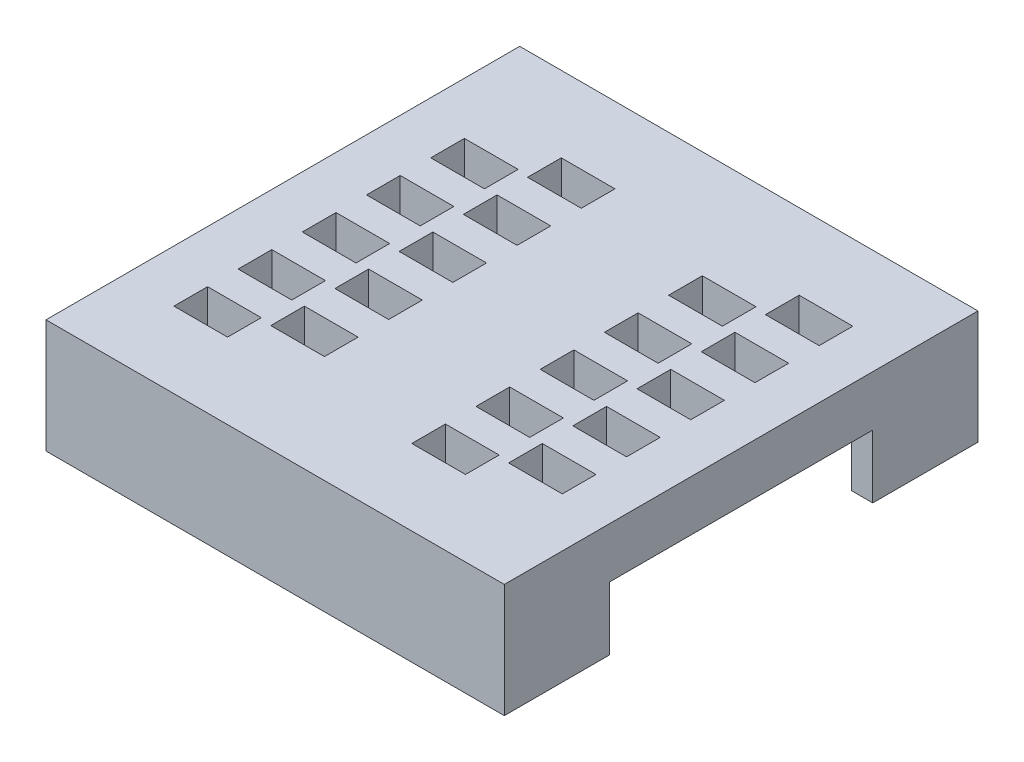
SolidWorks part; units mm, degrees
ref_plane "Спереди" through (0, 0, 0) normal (0, 0, 1) x (1, 0, 0)
ref_plane "Сверху" through (0, 0, 0) normal (0, 1, 0) x (1, 0, 0)
ref_plane "Справа" through (0, 0, 0) normal (1, 0, 0) x (0, 0, -1)
sketch "Эскиз1" plane through (0, 0, 0) normal (0, 1, 0) x (1, 0, 0)
  line L0 (2.8031, 2.5812) -> (46.3427, 2.5812)
  line L1 (46.3427, 2.5812) -> (46.3427, 47.5812)
  line L2 (46.3427, 47.5812) -> (2.8031, 47.5812)
  line L3 (2.8031, 47.5812) -> (2.8031, 2.5812)
  line L5 (13.9531, 37.1809) -> (19.0531, 37.1809)
  line L6 (13.9531, 37.1809) -> (13.9531, 40.3809)
  line L7 (13.9531, 40.3809) -> (19.0531, 40.3809)
  line L8 (19.0531, 37.1809) -> (19.0531, 40.3809)
  line L9 (13.9531, 37.1809) -> (19.0531, 40.3809) construction
  line L10 (13.9531, 40.3809) -> (19.0531, 37.1809) construction
  line L11 (36.5531, 37.1809) -> (41.6531, 37.1809)
  line L12 (36.5531, 37.1809) -> (36.5531, 40.3809)
  line L13 (36.5531, 40.3809) -> (41.6531, 40.3809)
  line L14 (41.6531, 37.1809) -> (41.6531, 40.3809)
  line L15 (36.5531, 37.1809) -> (41.6531, 40.3809) construction
  line L16 (36.5531, 40.3809) -> (41.6531, 37.1809) construction
  line L17 (7.7531, 34.1809) -> (12.8531, 34.1809)
  line L18 (7.7531, 34.1809) -> (7.7531, 37.3809)
  line L19 (7.7531, 37.3809) -> (12.8531, 37.3809)
  line L20 (12.8531, 34.1809) -> (12.8531, 37.3809)
  line L21 (7.7531, 34.1809) -> (12.8531, 37.3809) construction
  line L22 (7.7531, 37.3809) -> (12.8531, 34.1809) construction
  line L23 (30.3531, 34.1809) -> (35.4531, 34.1809)
  line L24 (30.3531, 34.1809) -> (30.3531, 37.3809)
  line L25 (30.3531, 37.3809) -> (35.4531, 37.3809)
  line L26 (35.4531, 34.1809) -> (35.4531, 37.3809)
  line L27 (30.3531, 34.1809) -> (35.4531, 37.3809) construction
  line L28 (30.3531, 37.3809) -> (35.4531, 34.1809) construction
  line L29 (13.9531, 31.0809) -> (19.0531, 31.0809)
  line L30 (13.9531, 31.0809) -> (13.9531, 34.2809)
  line L31 (13.9531, 34.2809) -> (19.0531, 34.2809)
  line L32 (19.0531, 31.0809) -> (19.0531, 34.2809)
  line L33 (13.9531, 31.0809) -> (19.0531, 34.2809) construction
  line L34 (13.9531, 34.2809) -> (19.0531, 31.0809) construction
  line L35 (36.5531, 31.0809) -> (41.6531, 31.0809)
  line L36 (36.5531, 31.0809) -> (36.5531, 34.2809)
  line L37 (36.5531, 34.2809) -> (41.6531, 34.2809)
  line L38 (41.6531, 31.0809) -> (41.6531, 34.2809)
  line L39 (36.5531, 31.0809) -> (41.6531, 34.2809) construction
  line L40 (36.5531, 34.2809) -> (41.6531, 31.0809) construction
  line L41 (7.7531, 28.0809) -> (12.8531, 28.0809)
  line L42 (7.7531, 28.0809) -> (7.7531, 31.2809)
  line L43 (7.7531, 31.2809) -> (12.8531, 31.2809)
  line L44 (12.8531, 28.0809) -> (12.8531, 31.2809)
  line L45 (7.7531, 28.0809) -> (12.8531, 31.2809) construction
  line L46 (7.7531, 31.2809) -> (12.8531, 28.0809) construction
  line L47 (30.3531, 28.0809) -> (35.4531, 28.0809)
  line L48 (30.3531, 28.0809) -> (30.3531, 31.2809)
  line L49 (30.3531, 31.2809) -> (35.4531, 31.2809)
  line L50 (35.4531, 28.0809) -> (35.4531, 31.2809)
  line L51 (30.3531, 28.0809) -> (35.4531, 31.2809) construction
  line L52 (30.3531, 31.2809) -> (35.4531, 28.0809) construction
  line L53 (41.6531, 24.9809) -> (36.5531, 24.9809)
  line L54 (41.6531, 24.9809) -> (41.6531, 28.1809)
  line L55 (41.6531, 28.1809) -> (36.5531, 28.1809)
  line L56 (36.5531, 24.9809) -> (36.5531, 28.1809)
  line L57 (41.6531, 24.9809) -> (36.5531, 28.1809) construction
  line L58 (41.6531, 28.1809) -> (36.5531, 24.9809) construction
  line L59 (19.0531, 24.9809) -> (13.9531, 24.9809)
  line L60 (19.0531, 24.9809) -> (19.0531, 28.1809)
  line L61 (19.0531, 28.1809) -> (13.9531, 28.1809)
  line L62 (13.9531, 24.9809) -> (13.9531, 28.1809)
  line L63 (19.0531, 24.9809) -> (13.9531, 28.1809) construction
  line L64 (19.0531, 28.1809) -> (13.9531, 24.9809) construction
  line L65 (7.7531, 21.9809) -> (12.8531, 21.9809)
  line L66 (7.7531, 21.9809) -> (7.7531, 25.1809)
  line L67 (7.7531, 25.1809) -> (12.8531, 25.1809)
  line L68 (12.8531, 21.9809) -> (12.8531, 25.1809)
  line L69 (7.7531, 21.9809) -> (12.8531, 25.1809) construction
  line L70 (7.7531, 25.1809) -> (12.8531, 21.9809) construction
  line L71 (30.3531, 21.9809) -> (35.4531, 21.9809)
  line L72 (30.3531, 21.9809) -> (30.3531, 25.1809)
  line L73 (30.3531, 25.1809) -> (35.4531, 25.1809)
  line L74 (35.4531, 21.9809) -> (35.4531, 25.1809)
  line L75 (30.3531, 21.9809) -> (35.4531, 25.1809) construction
  line L76 (30.3531, 25.1809) -> (35.4531, 21.9809) construction
  line L77 (41.6531, 18.8809) -> (36.5531, 18.8809)
  line L78 (41.6531, 18.8809) -> (41.6531, 22.0809)
  line L79 (41.6531, 22.0809) -> (36.5531, 22.0809)
  line L80 (36.5531, 18.8809) -> (36.5531, 22.0809)
  line L81 (41.6531, 18.8809) -> (36.5531, 22.0809) construction
  line L82 (41.6531, 22.0809) -> (36.5531, 18.8809) construction
  line L83 (19.0531, 18.8809) -> (13.9531, 18.8809)
  line L84 (10.3031, 49.6407) -> (10.3031, -1.549) construction
  line L85 (16.5031, 49.6407) -> (16.5031, -1.4408) construction
  line L86 (32.9031, 49.6407) -> (32.9031, -1.6572) construction
  line L87 (39.1031, 49.6407) -> (39.1031, -2.7395) construction
  line L88 (1.0994, 38.7809) -> (49.6918, 38.7809) construction
  line L89 (1.0994, 35.7809) -> (49.6918, 35.7809) construction
  line L90 (49.6918, 32.6809) -> (1.0994, 32.6809) construction
  line L91 (1.0994, 29.6809) -> (49.6918, 29.6809) construction
  line L92 (49.6918, 26.5809) -> (1.0994, 26.5809) construction
  line L93 (0.7747, 23.5809) -> (49.6918, 23.5809) construction
  line L94 (49.6918, 20.4809) -> (0.7747, 20.4809) construction
  line L95 (0.7747, 17.4809) -> (49.6918, 17.4809) construction
  line L96 (49.6918, 14.3809) -> (0.7747, 14.3809) construction
  line L97 (-6.1228, 11.3809) -> (51.4369, 11.3809) construction
  line L98 (19.0531, 18.8809) -> (19.0531, 22.0809)
  line L99 (19.0531, 22.0809) -> (13.9531, 22.0809)
  line L100 (13.9531, 18.8809) -> (13.9531, 22.0809)
  line L101 (19.0531, 18.8809) -> (13.9531, 22.0809) construction
  line L102 (19.0531, 22.0809) -> (13.9531, 18.8809) construction
  line L103 (35.4531, 15.8809) -> (30.3531, 15.8809)
  line L104 (35.4531, 15.8809) -> (35.4531, 19.0809)
  line L105 (35.4531, 19.0809) -> (30.3531, 19.0809)
  line L106 (30.3531, 15.8809) -> (30.3531, 19.0809)
  line L107 (35.4531, 15.8809) -> (30.3531, 19.0809) construction
  line L108 (35.4531, 19.0809) -> (30.3531, 15.8809) construction
  line L109 (12.8531, 15.8809) -> (7.7531, 15.8809)
  line L110 (12.8531, 15.8809) -> (12.8531, 19.0809)
  line L111 (12.8531, 19.0809) -> (7.7531, 19.0809)
  line L112 (7.7531, 15.8809) -> (7.7531, 19.0809)
  line L113 (12.8531, 15.8809) -> (7.7531, 19.0809) construction
  line L114 (12.8531, 19.0809) -> (7.7531, 15.8809) construction
  line L115 (19.0531, 12.7809) -> (13.9531, 12.7809)
  line L116 (19.0531, 12.7809) -> (19.0531, 15.9809)
  line L117 (19.0531, 15.9809) -> (13.9531, 15.9809)
  line L118 (13.9531, 12.7809) -> (13.9531, 15.9809)
  line L119 (19.0531, 12.7809) -> (13.9531, 15.9809) construction
  line L120 (19.0531, 15.9809) -> (13.9531, 12.7809) construction
  line L121 (7.7531, 9.7809) -> (12.8531, 9.7809)
  line L122 (7.7531, 9.7809) -> (7.7531, 12.9809)
  line L123 (7.7531, 12.9809) -> (12.8531, 12.9809)
  line L124 (12.8531, 9.7809) -> (12.8531, 12.9809)
  line L125 (7.7531, 9.7809) -> (12.8531, 12.9809) construction
  line L126 (7.7531, 12.9809) -> (12.8531, 9.7809) construction
  line L127 (30.3531, 9.7809) -> (35.4531, 9.7809)
  line L128 (30.3531, 9.7809) -> (30.3531, 12.9809)
  line L129 (30.3531, 12.9809) -> (35.4531, 12.9809)
  line L130 (35.4531, 9.7809) -> (35.4531, 12.9809)
  line L131 (30.3531, 9.7809) -> (35.4531, 12.9809) construction
  line L132 (30.3531, 12.9809) -> (35.4531, 9.7809) construction
  line L133 (36.5531, 12.7809) -> (41.6531, 12.7809)
  line L134 (36.5531, 12.7809) -> (36.5531, 15.9809)
  line L135 (36.5531, 15.9809) -> (41.6531, 15.9809)
  line L136 (41.6531, 12.7809) -> (41.6531, 15.9809)
  line L137 (36.5531, 12.7809) -> (41.6531, 15.9809) construction
  line L138 (36.5531, 15.9809) -> (41.6531, 12.7809) construction
  point P7 (16.5031, 38.7809)
  point P12 (39.1031, 38.7809)
  point P17 (10.3031, 35.7809)
  point P22 (32.9031, 35.7809)
  point P27 (16.5031, 32.6809)
  point P32 (39.1031, 32.6809)
  point P37 (10.3031, 29.6809)
  point P42 (32.9031, 29.6809)
  point P47 (39.1031, 26.5809)
  point P52 (16.5031, 26.5809)
  point P57 (10.3031, 23.5809)
  point P62 (32.9031, 23.5809)
  point P67 (39.1031, 20.4809)
  point P72 (16.5031, 20.4809)
  point P77 (32.9031, 17.4809)
  point P82 (10.3031, 17.4809)
  point P112 (16.5031, 14.3809)
  point P117 (10.3031, 11.3809)
  point P122 (32.9031, 11.3809)
  point P127 (39.1031, 14.3809)
  dimension "D1" = 43.5396
  dimension "D2" = 45
  dimension "D3" = 7.5
  dimension "D4" = 6.2
  dimension "D5" = 16.4
  dimension "D6" = 6.2
  dimension "D7" = 8.8003
  dimension "D8" = 3
  dimension "D9" = 3.1
  dimension "D10" = 3
  dimension "D11" = 3.1
  dimension "D12" = 3
  dimension "D13" = 3.1
  dimension "D14" = 3
  dimension "D15" = 3.1
  dimension "D16" = 3
  dimension "D17" = 3.2
  dimension "D18" = 5.1
extrude "Бобышка-Вытянуть1" add sketch "Эскиз1" along normal blind 3.2
sketch "Эскиз2" plane through (0, 0, 0) normal (0, 1, 0) x (1, 0, 0)
  line L1 (2.8031, 47.5812) -> (46.3427, 47.5812)
  line L2 (2.8031, 47.5812) -> (2.8031, 2.5812)
  line L3 (2.8031, 2.5812) -> (46.3427, 2.5812)
  line L4 (-1.1216, 42.5812) -> (57.6795, 42.5812) construction
  line L5 (46.3427, 47.5812) -> (46.3427, 2.5812)
  line L65 (-1.6798, 7.5812) -> (52.4692, 7.5812) construction
  line L66 (7.8031, 55.0464) -> (7.8031, -0.7774) construction
  line L67 (41.3427, 54.5812) -> (41.3427, -0.6844) construction
  line L68 (2.8031, 47.5812) -> (2.8031, 2.5812) construction
  line L69 (46.3427, 2.5812) -> (46.3427, 47.5812) construction
  line L70 (46.3427, 47.5812) -> (2.8031, 47.5812) construction
  line L71 (2.8031, 2.5812) -> (46.3427, 2.5812) construction
  line L72 (16.5031, 50.8599) -> (16.5031, 0.0003) construction
  line L89 (32.9031, 50.8599) -> (32.9031, -1.0562) construction
  line L90 (-0.3772, 38.7812) -> (21.6731, 38.7812) construction
  line L91 (21.6731, 32.6812) -> (-0.3772, 32.6812) construction
  line L92 (21.6731, 26.5812) -> (-0.3772, 26.5812) construction
  line L93 (21.6731, 20.4812) -> (-0.3772, 20.4812) construction
  line L94 (21.6731, 14.3812) -> (-0.3772, 14.3812) construction
  line L95 (26.2321, 11.3812) -> (49.1198, 11.3812) construction
  line L96 (26.2321, 17.4812) -> (49.1198, 17.4812) construction
  line L97 (26.2321, 23.5812) -> (49.1198, 23.5812) construction
  line L98 (26.2321, 29.6812) -> (49.1198, 29.6812) construction
  line L99 (25.953, 35.7812) -> (49.1198, 35.7812) construction
  line L101 (13.7031, 35.9812) -> (19.3031, 35.9812)
  line L102 (13.7031, 35.9812) -> (13.7031, 41.5812)
  line L103 (13.7031, 41.5812) -> (19.3031, 41.5812)
  line L104 (19.3031, 35.9812) -> (19.3031, 41.5812)
  line L105 (13.7031, 35.9812) -> (19.3031, 41.5812) construction
  line L106 (13.7031, 41.5812) -> (19.3031, 35.9812) construction
  line L107 (13.7031, 29.8241) -> (19.3031, 29.8241)
  line L108 (13.7031, 29.8241) -> (13.7031, 35.4241)
  line L109 (13.7031, 35.4241) -> (19.3031, 35.4241)
  line L110 (19.3031, 29.8241) -> (19.3031, 35.4241)
  line L111 (13.7031, 29.8241) -> (19.3031, 35.4241) construction
  line L112 (13.7031, 35.4241) -> (19.3031, 29.8241) construction
  line L113 (13.7031, 23.7812) -> (19.3031, 23.7812)
  line L114 (13.7031, 23.7812) -> (13.7031, 29.3812)
  line L115 (13.7031, 29.3812) -> (19.3031, 29.3812)
  line L116 (19.3031, 23.7812) -> (19.3031, 29.3812)
  line L117 (13.7031, 23.7812) -> (19.3031, 29.3812) construction
  line L118 (13.7031, 29.3812) -> (19.3031, 23.7812) construction
  line L119 (13.7031, 17.6812) -> (19.3031, 17.6812)
  line L120 (13.7031, 17.6812) -> (13.7031, 23.2812)
  line L121 (13.7031, 23.2812) -> (19.3031, 23.2812)
  line L122 (19.3031, 17.6812) -> (19.3031, 23.2812)
  line L123 (13.7031, 17.6812) -> (19.3031, 23.2812) construction
  line L124 (13.7031, 23.2812) -> (19.3031, 17.6812) construction
  line L125 (13.7031, 11.5812) -> (19.3031, 11.5812)
  line L126 (13.7031, 11.5812) -> (13.7031, 17.1812)
  line L127 (13.7031, 17.1812) -> (19.3031, 17.1812)
  line L128 (19.3031, 11.5812) -> (19.3031, 17.1812)
  line L129 (13.7031, 11.5812) -> (19.3031, 17.1812) construction
  line L130 (13.7031, 17.1812) -> (19.3031, 11.5812) construction
  line L131 (35.7031, 8.5812) -> (30.1031, 8.5812)
  line L132 (35.7031, 8.5812) -> (35.7031, 14.1812)
  line L133 (35.7031, 14.1812) -> (30.1031, 14.1812)
  line L134 (30.1031, 8.5812) -> (30.1031, 14.1812)
  line L135 (35.7031, 8.5812) -> (30.1031, 14.1812) construction
  line L136 (35.7031, 14.1812) -> (30.1031, 8.5812) construction
  line L137 (35.7031, 14.6812) -> (30.1031, 14.6812)
  line L138 (35.7031, 14.6812) -> (35.7031, 20.2812)
  line L139 (35.7031, 20.2812) -> (30.1031, 20.2812)
  line L140 (30.1031, 14.6812) -> (30.1031, 20.2812)
  line L141 (35.7031, 14.6812) -> (30.1031, 20.2812) construction
  line L142 (35.7031, 20.2812) -> (30.1031, 14.6812) construction
  line L143 (35.7031, 20.7812) -> (30.1031, 20.7812)
  line L144 (35.7031, 20.7812) -> (35.7031, 26.3812)
  line L145 (35.7031, 26.3812) -> (30.1031, 26.3812)
  line L146 (30.1031, 20.7812) -> (30.1031, 26.3812)
  line L147 (35.7031, 20.7812) -> (30.1031, 26.3812) construction
  line L148 (35.7031, 26.3812) -> (30.1031, 20.7812) construction
  line L149 (35.7031, 26.8812) -> (30.1031, 26.8812)
  line L150 (35.7031, 26.8812) -> (35.7031, 32.4812)
  line L151 (35.7031, 32.4812) -> (30.1031, 32.4812)
  line L152 (30.1031, 26.8812) -> (30.1031, 32.4812)
  line L153 (35.7031, 26.8812) -> (30.1031, 32.4812) construction
  line L154 (35.7031, 32.4812) -> (30.1031, 26.8812) construction
  line L155 (35.7031, 32.9812) -> (30.1031, 32.9812)
  line L156 (35.7031, 32.9812) -> (35.7031, 38.5812)
  line L157 (35.7031, 38.5812) -> (30.1031, 38.5812)
  line L158 (30.1031, 32.9812) -> (30.1031, 38.5812)
  line L159 (35.7031, 32.9812) -> (30.1031, 38.5812) construction
  line L160 (35.7031, 38.5812) -> (30.1031, 32.9812) construction
  circle A4 centre (7.8031, 42.5812) radius 0.5
  circle A5 centre (41.3427, 42.5812) radius 0.5
  circle A6 centre (41.3427, 7.5812) radius 0.5
  circle A7 centre (7.8031, 7.5812) radius 0.5
  point P142 (16.5031, 38.7812)
  point P147 (16.5031, 32.6241)
  point P148 (16.5031, 32.6241)
  point P152 (16.5031, 26.5812)
  point P157 (16.5031, 20.4812)
  point P162 (16.5031, 14.3812)
  point P167 (32.9031, 11.3812)
  point P172 (32.9031, 17.4812)
  point P177 (32.9031, 23.5812)
  point P182 (32.9031, 29.6812)
  point P187 (32.9031, 35.7812)
  dimension "D26" = 1
  dimension "D22" = 5
  dimension "D23" = 5
  dimension "D24" = 5
  dimension "D25" = 5
  dimension "D27" = 6.8
  dimension "D28" = 6.1
  dimension "D29" = 6.1
  dimension "D30" = 6.1
  dimension "D31" = 6.1
  dimension "D32" = 3.8
  dimension "D33" = 6.1
  dimension "D34" = 6.1
  dimension "D35" = 6.1
  dimension "D36" = 6.1
  dimension "D37" = 5.6
  dimension "D38" = 5.6
extrude "Бобышка-Вытянуть3" add sketch "Эскиз2" against normal blind 0.6
sketch "Эскиз3" plane through (0, -0.6, 0) normal (0, -1, 0) x (1, 0, 0)
  circle A0 centre (7.8031, -7.5812) radius 0.5
  circle A1 centre (41.3427, -7.5812) radius 0.5
  circle A2 centre (7.8031, -42.5812) radius 0.5
  circle A3 centre (41.3427, -42.5812) radius 0.5
  circle A4 centre (7.8031, -7.5812) radius 5
  circle A5 centre (41.3427, -7.5812) radius 5
  circle A6 centre (41.3427, -42.5812) radius 5
  circle A7 centre (7.8031, -42.5812) radius 5
  point P15 (41.3427, -42.5812)
  dimension "D1" = 10
  dimension "D2" = 1
extrude "Бобышка-Вытянуть4" add sketch "Эскиз3" along normal blind 1
sketch "Эскиз4" plane through (0, -0.6, 0) normal (0, -1, 0) x (1, 0, 0)
  line L1 (2.8031, -47.5812) -> (46.3427, -47.5812)
  line L2 (2.8031, -47.5812) -> (2.8031, -2.5812)
  line L3 (2.8031, -2.5812) -> (46.3427, -2.5812)
  line L4 (46.3427, -47.5812) -> (46.3427, -2.5812)
  line L5 (4.8031, -4.5812) -> (44.3427, -4.5812)
  line L6 (4.8031, -4.5812) -> (4.8031, -45.5812)
  line L7 (4.8031, -45.5812) -> (44.3427, -45.5812)
  line L8 (44.3427, -4.5812) -> (44.3427, -45.5812)
  dimension "D1" = 2
  dimension "D2" = 2
  dimension "D3" = 2
  dimension "D4" = 2
extrude "Бобышка-Вытянуть6" add sketch "Эскиз4" along normal blind 7
sketch "Эскиз6" plane through (0, -7.6, 0) normal (0, -1, 0) x (1, 0, 0)
  line L0 (2.8031, -2.5812) -> (2.8031, -47.5812) construction
  line L1 (2.8031, -12.5812) -> (4.8031, -12.5812)
  line L2 (2.8031, -12.5812) -> (2.8031, -37.5812)
  line L3 (2.8031, -37.5812) -> (4.8031, -37.5812)
  line L4 (4.8031, -12.5812) -> (4.8031, -37.5812)
  line L5 (4.8031, -11.5812) -> (4.8031, -38.5812) construction
  line L6 (44.3427, -38.5812) -> (44.3427, -11.5812) construction
  line L7 (44.3427, -12.5812) -> (46.3427, -12.5812)
  line L8 (44.3427, -12.5812) -> (44.3427, -37.5812)
  line L9 (44.3427, -37.5812) -> (46.3427, -37.5812)
  line L10 (46.3427, -12.5812) -> (46.3427, -37.5812)
  line L11 (46.3427, -47.5812) -> (46.3427, -2.5812) construction
  line L12 (46.3427, -2.5812) -> (2.8031, -2.5812) construction
  line L13 (2.8031, -47.5812) -> (46.3427, -47.5812) construction
  point P18 (3.8031, -37.5812)
  point P21 (45.3427, -12.5812)
  dimension "D1" = 10
  dimension "D2" = 10
  dimension "D3" = 10
  dimension "D4" = 10
extrude "Вырез-Вытянуть2" cut sketch "Эскиз6" against normal blind 6
sketch "Эскиз8" plane through (0, -0.6, 0) normal (0, -1, 0) x (1, 0, 0)
  line L0 (22.8031, -1.1632) -> (22.8031, -50.5324) construction
  line L1 (2.8031, -12.5812) -> (2.8031, -37.5812) construction
  text T0 "<b>dip56245</b>"
  dimension "D1" = 20
extrude "Вырез-Вытянуть4" cut sketch "Эскиз8" against normal blind 0.2
